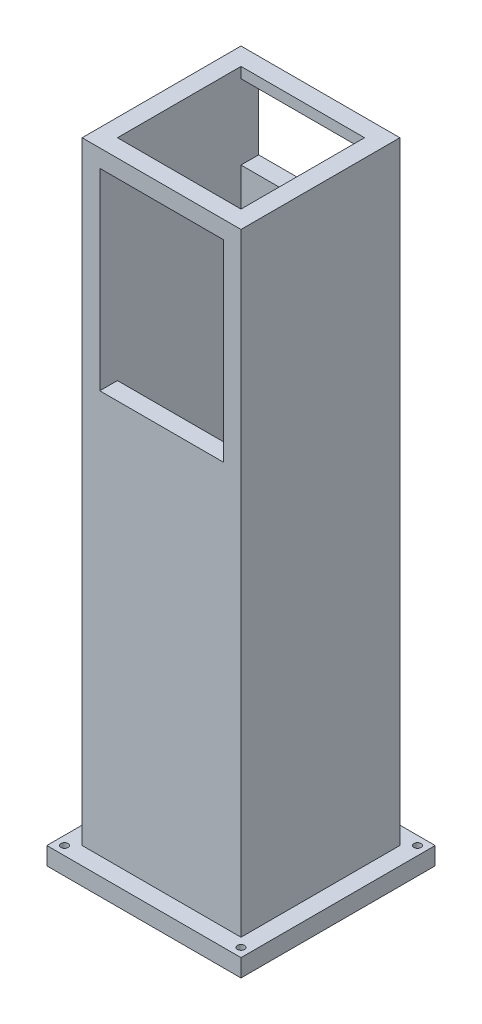
SolidWorks part; units mm, degrees
ref_plane "Alzado" through (0, 0, 0) normal (0, 0, 1) x (1, 0, 0)
ref_plane "Planta" through (0, 0, 0) normal (0, 1, 0) x (1, 0, 0)
ref_plane "Vista lateral" through (0, 0, 0) normal (1, 0, 0) x (0, 0, -1)
sketch "Croquis1" plane through (0, 0, 0) normal (0, 1, 0) x (1, 0, 0)
  line L1 (-22.5, -22.5) -> (22.5, -22.5)
  line L2 (-22.5, -22.5) -> (-22.5, 22.5)
  line L3 (-22.5, 22.5) -> (22.5, 22.5)
  line L4 (22.5, -22.5) -> (22.5, 22.5)
  line L5 (-22.5, -22.5) -> (22.5, 22.5) construction
  line L6 (-22.5, 22.5) -> (22.5, -22.5) construction
  point P0 (0, 0)
  dimension "D1" = 45
  dimension "D2" = 45
extrude "Saliente-Extruir1" add sketch "Croquis1" along normal blind 300
sketch "Croquis4" plane through (-22.5, 0, 0) normal (-1, 0, 0) x (0, 0, 1)
  line L1 (22.5, 300) -> (22.5, 0) construction
  line L3 (30.25, 0) -> (-30.25, 0) construction
  line L5 (4.5, 0) -> (4.5, 34)
  line L6 (4.5, 34) -> (22.5, 34)
  line L8 (22.5, 34) -> (22.5, 0)
  line L9 (22.5, 0) -> (4.5, 0)
  dimension "D4" = 34
extrude "Cortar-Extruir2" cut sketch "Croquis4" against normal through all
sketch "Croquis7" plane through (0, 0, 22.5) normal (0, 0, 1) x (1, 0, 0)
  line L0 (0, -30.25) -> (0, 30.25) construction
  line L1 (-22.5, 246.3879) -> (22.5, 246.3879)
  line L2 (-22.5, 246.3879) -> (-22.5, 273.6121)
  line L3 (-22.5, 273.6121) -> (22.5, 273.6121)
  line L4 (22.5, 246.3879) -> (22.5, 273.6121)
  line L5 (-22.5, 246.3879) -> (22.5, 273.6121) construction
  line L6 (-22.5, 273.6121) -> (22.5, 246.3879) construction
  line L7 (22.5, 300) -> (22.5, 34) construction
  point P0 (0, 260)
  dimension "D1" = 260
sketch "Croquis8" plane through (0, 300, 0) normal (0, 1, 0) x (1, 0, 0)
  line L0 (22.5, -22.5) -> (22.5, 22.5) construction
  line L1 (-17.5, -17.5) -> (17.5, -17.5)
  line L2 (-17.5, -17.5) -> (-17.5, 17.5)
  line L3 (-17.5, 17.5) -> (17.5, 17.5)
  line L4 (17.5, -17.5) -> (17.5, 17.5)
  line L5 (-17.5, -17.5) -> (17.5, 17.5) construction
  line L6 (-17.5, 17.5) -> (17.5, -17.5) construction
  line L7 (22.5, 22.5) -> (-22.5, 22.5) construction
  point P0 (0, 0)
  dimension "D1" = 5
  dimension "D2" = 5
extrude "Cortar-Extruir3" cut sketch "Croquis8" against normal through all contours L3 L4 L1 L2
sketch "Croquis9" plane through (0, 0, -22.5) normal (0, 0, -1) x (-1, 0, 0)
  line L0 (22.5, 273.6121) -> (-22.5, 246.3879) construction
  line L1 (-17.5, 249.4128) -> (17.5, 249.4128)
  line L2 (-17.5, 249.4128) -> (-17.5, 270.5872)
  line L3 (-17.5, 270.5872) -> (17.5, 270.5872)
  line L4 (17.5, 249.4128) -> (17.5, 270.5872)
  line L5 (-17.5, 249.4128) -> (17.5, 270.5872) construction
  line L6 (-17.5, 270.5872) -> (17.5, 249.4128) construction
  line L7 (22.5, 246.3879) -> (22.5, 273.6121) construction
  point P0 (0, 260)
  point P10 (22.5, 260)
  dimension "D1" = 5
extrude "Cortar-Extruir4" cut sketch "Croquis9" against normal blind 10 contours L4 L3 L2 L1
sketch "Croquis10" plane through (0, 0, 22.5) normal (0, 0, 1) x (1, 0, 0)
  circle A0 centre (0, 260) radius 1
  dimension "D1" = 2
extrude "Cortar-Extruir5" cut sketch "Croquis10" against normal blind 10
sketch "Croquis17" plane through (0, 0, 22.5) normal (0, 0, 1) x (1, 0, 0)
  line L0 (-22.5, 246.3879) -> (-22.5, 273.6121) construction
  line L1 (-17.5, 268.6121) -> (17.5, 268.6121)
  line L2 (-17.5, 268.6121) -> (-17.5, 214.0387)
  line L3 (-17.5, 214.0387) -> (17.5, 214.0387)
  line L4 (17.5, 268.6121) -> (17.5, 214.0387)
  line L5 (22.5, 246.3879) -> (22.5, 273.6121) construction
  line L6 (-22.5, 273.6121) -> (22.5, 273.6121) construction
  dimension "D1" = 5
  dimension "D2" = 5
  dimension "D3" = 5
extrude "Cortar-Extruir9" cut sketch "Croquis17" against normal blind 10
sketch "Croquis11" plane through (0, 0, 22.5) normal (0, 0, 1) x (1, 0, 0)
  line L0 (22.5, 300) -> (22.5, 34) construction
  line L1 (-22.5, 300) -> (22.5, 300)
  line L2 (-22.5, 300) -> (-22.5, 273.6121)
  line L3 (-22.5, 273.6121) -> (22.5, 273.6121)
  line L4 (22.5, 300) -> (22.5, 273.6121)
  line L5 (-22.5, 273.6121) -> (22.5, 273.6121) construction
  dimension "D1" = 0
extrude "Cortar-Extruir6" cut sketch "Croquis11" against normal through all
sketch "Croquis12" plane through (0, 0, 22.5) normal (0, 0, 1) x (1, 0, 0)
  line L0 (-22.5, 267.3717) -> (22.5, 246.3879)
  line L1 (-22.5, 246.3879) -> (-22.5, 273.6121) construction
  line L2 (-22.5, 246.3879) -> (22.5, 246.3879) construction
  dimension "D1" = 25
sketch "Croquis13" plane through (0, 0, 0) normal (1, 0, 0) x (0, 0, -1)
  line L0 (-22.5, 273.6121) -> (-22.5, 34) construction
  line L1 (-22.5, 100) -> (22.5, 100)
  line L2 (-22.5, 100) -> (-22.5, 0)
  line L3 (-22.5, 0) -> (22.5, 0)
  line L4 (22.5, 100) -> (22.5, 0)
  line L5 (24.75, 0) -> (-24.75, 0) construction
  line L6 (22.5, 273.6121) -> (22.5, 0) construction
  dimension "D1" = 100
extrude "Cortar-Extruir7" cut sketch "Croquis13" against normal through all both and the other way through all
sketch "Croquis14" plane through (0, 100, 0) normal (0, -1, 0) x (1, 0, 0)
  line L1 (-27.5, -27.5) -> (27.5, -27.5)
  line L2 (-27.5, -27.5) -> (-27.5, 27.5)
  line L3 (-27.5, 27.5) -> (27.5, 27.5)
  line L4 (27.5, -27.5) -> (27.5, 27.5)
  line L5 (-27.5, -27.5) -> (27.5, 27.5) construction
  line L6 (-27.5, 27.5) -> (27.5, -27.5) construction
  point P0 (0, 0)
  dimension "D1" = 27.5
  dimension "D2" = 27.5
extrude "Saliente-Extruir2" add sketch "Croquis14" along normal blind 5 contours L3 L4 L1 L2
sketch "Croquis16" plane through (0, 95, 0) normal (0, -1, 0) x (1, 0, 0)
  circle A0 centre (25, 25) radius 1
  circle A1 centre (-25, 25) radius 1
  circle A2 centre (-25, -25) radius 1
  circle A3 centre (25, -25) radius 1
  dimension "D1" = 2
  dimension "D2" = 2.5
  dimension "D3" = 2.5
  dimension "D4" = 2.5
  dimension "D5" = 2.5
extrude "Cortar-Extruir8" cut sketch "Croquis16" against normal through all both
